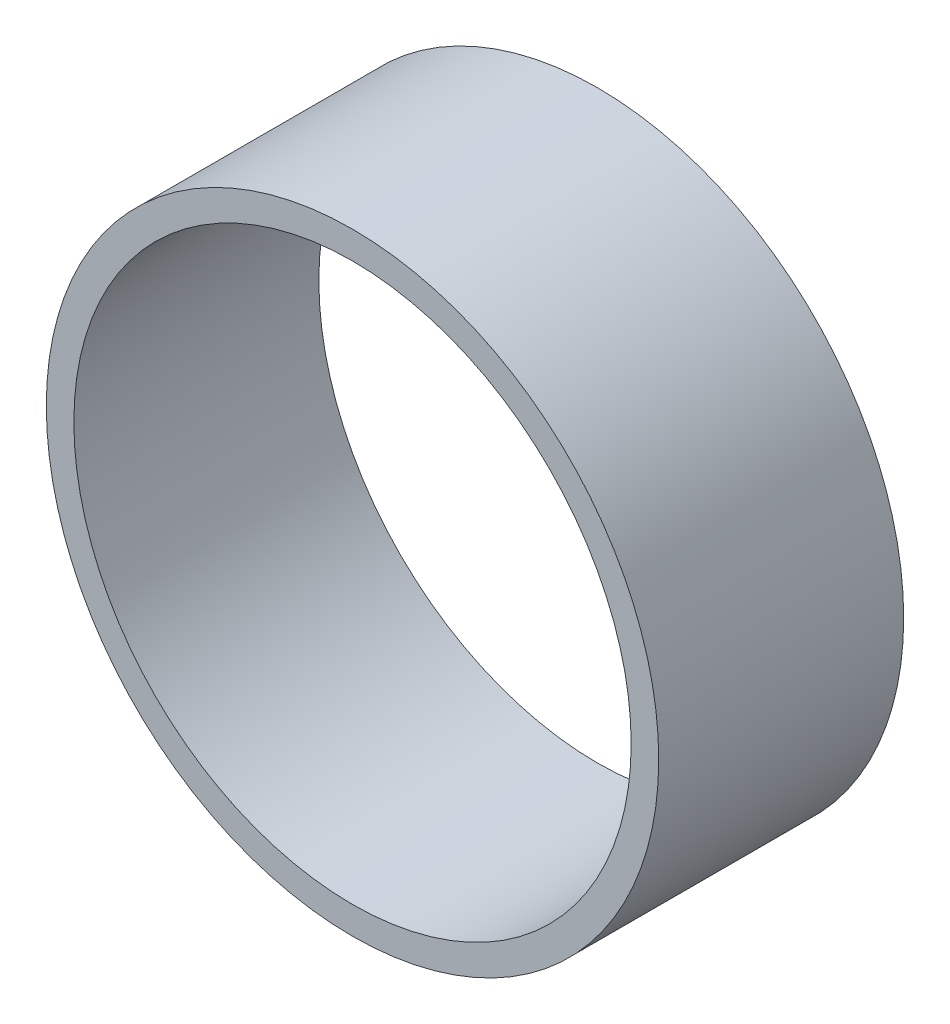
SolidWorks part; units mm, degrees
ref_plane "Front Plane" through (0, 0, 0) normal (0, 0, 1) x (1, 0, 0)
ref_plane "Top Plane" through (0, 0, 0) normal (0, 1, 0) x (1, 0, 0)
ref_plane "Right Plane" through (0, 0, 0) normal (1, 0, 0) x (0, 0, -1)
sketch "Sketch1" plane through (0, 0, 0) normal (0, 0, 1) x (1, 0, 0)
  circle A0 centre (0, 0) radius 4.55
  circle A1 centre (0, 0) radius 5
  dimension "D1" = 9.1
  dimension "D2" = 10
extrude "Boss-Extrude1" add sketch "Sketch1" along normal blind 4
